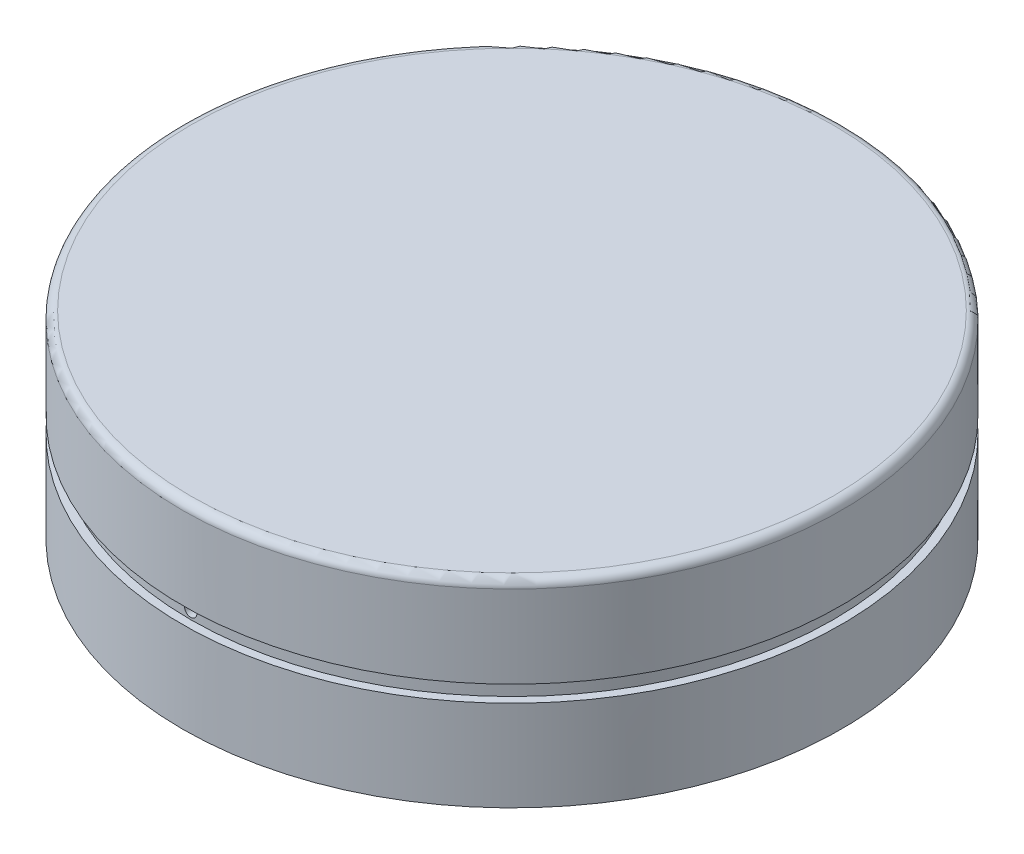
SolidWorks part; units mm, degrees
ref_plane "Front Plane" through (0, 0, 0) normal (0, 0, 1) x (1, 0, 0)
ref_plane "Top Plane" through (0, 0, 0) normal (0, 1, 0) x (1, 0, 0)
ref_plane "Right Plane" through (0, 0, 0) normal (1, 0, 0) x (0, 0, -1)
sketch "Sketch2" plane through (0, 0, 0) normal (0, 1, 0) x (1, 0, 0)
  circle A0 centre (0, 0) radius 20
  dimension "D1" = 40
extrude "Boss-Extrude1" add sketch "Sketch2" along normal mid plane 12 contours A0
sketch "Sketch3" plane through (0, -6, 0) normal (0, -1, 0) x (1, 0, 0)
  circle A0 centre (0, 0) radius 19
  circle A1 centre (0, 0) radius 20 construction
  dimension "D1" = 1
extrude "Cut-Extrude1" cut sketch "Sketch3" against normal offset from surface (11 mm away) 1 up to face at (0, 6, 20)
fillet "Fillet1" radius 0.5 1 edges at (0, 6, 20)
sketch "Sketch4" plane through (0, 5, 0) normal (0, -1, 0) x (1, 0, 0)
  circle A0 centre (0, 0) radius 2
  dimension "D1" = 4
sketch "Sketch5" plane through (0, 0, 0) normal (0, 0, 1) x (1, 0, 0)
  line L0 (20, 0.5) -> (19.5, 0.5)
  line L1 (20, -6) -> (20, 5.5) construction
  line L2 (19.5, 0.5) -> (19.5, -0.5)
  line L3 (19.5, -0.5) -> (20, -0.5)
  line L4 (0, 0) -> (20, 0) construction
  line L5 (20, 0.5) -> (20, -0.5)
  line L6 (0, 0) -> (0, 6) construction
  line L7 (19.5, 6) -> (-19.5, 6) construction
  dimension "D1" = 0.5
  dimension "D2" = 1
revolve "Cut-Revolve1" cut sketch "Sketch5" angle 360 about L6
sketch "Sketch6" plane through (0, 0, 0) normal (0, 0, 1) x (1, 0, 0)
  circle A0 centre (0, 0) radius 0.375
  dimension "D1" = 0.75
extrude "Cut-Extrude2" cut sketch "Sketch6" against normal through all both and the other way through all
sketch "Sketch7" plane through (0, 0, 0) normal (0, 0, 1) x (1, 0, 0)
  line L0 (0, 5) -> (0, -13.1004) construction
  line L1 (-2, 5) -> (2, 5) construction
  line L2 (5.9, 5) -> (5.9, 1)
  line L4 (7.9, 5) -> (5.9, 5)
  line L5 (5.9, 1) -> (6.9, 1)
  line L6 (6.9, 1) -> (7.9, 5)
  dimension "D1" = 5.9
  dimension "D2" = 4
  dimension "D3" = 2
  dimension "D4" = 1
revolve "Revolve1" add sketch "Sketch7" angle 360 about L0
equation "\"Tappet Diameter\" = 40mm"
equation "\"Tappet Length\"= 20mm"
equation "\"D1@Sketch2\"=\"Tappet Diameter\""
equation "\"Wall Thickness\"= 1mm"
equation "\"D1@Sketch3\"=\"Wall Thickness\""
equation "\"D1@Cut-Extrude1\"=\"Wall Thickness\""
equation "\"D1@Sketch5\"=\"Wall Thickness\"/2"
equation "\"D1@Sketch7\"=11.8/2"
